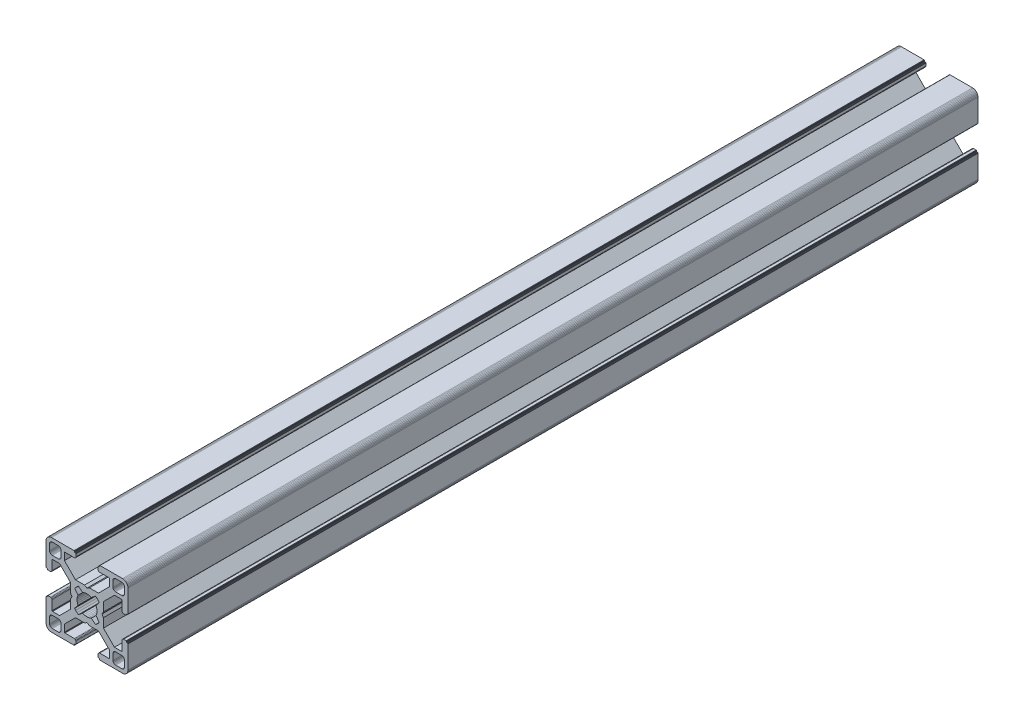
SolidWorks part; units mm, degrees
ref_plane "Front Plane" through (0, 0, 0) normal (0, 0, 1) x (1, 0, 0)
ref_plane "Top Plane" through (0, 0, 0) normal (0, 1, 0) x (1, 0, 0)
ref_plane "Right Plane" through (0, 0, 0) normal (1, 0, 0) x (0, 0, -1)
ref_plane "Plane1" through (0, 0, 0) normal (0, 0, 1) x (1, 0, 0)
sketch "Sketch1" plane through (0, 0, 0) normal (0, 0, 1) x (1, 0, 0)
  line L0 (28.3473, 29.9696) -> (28, 30)
  line L1 (28, 30) -> (19.75, 30)
  line L2 (19.75, 30) -> (19.7153, 29.997)
  line L3 (19.7153, 29.997) -> (19.6816, 29.9879)
  line L4 (19.6816, 29.9879) -> (19.65, 29.9732)
  line L5 (19.65, 29.9732) -> (19.6214, 29.9532)
  line L6 (19.6214, 29.9532) -> (19.5968, 29.9286)
  line L7 (19.5968, 29.9286) -> (19.5768, 29.9)
  line L8 (19.5768, 29.9) -> (19.5621, 29.8684)
  line L9 (19.5621, 29.8684) -> (19.553, 29.8347)
  line L10 (19.553, 29.8347) -> (19.55, 29.8)
  line L11 (19.55, 29.8) -> (19.55, 29.7)
  line L12 (19.55, 29.7) -> (19.547, 29.6653)
  line L13 (19.547, 29.6653) -> (19.5379, 29.6316)
  line L14 (19.5379, 29.6316) -> (19.5232, 29.6)
  line L15 (19.5232, 29.6) -> (19.5032, 29.5714)
  line L16 (19.5032, 29.5714) -> (19.4786, 29.5468)
  line L17 (19.4786, 29.5468) -> (19.45, 29.5268)
  line L18 (19.45, 29.5268) -> (19.4184, 29.5121)
  line L19 (19.4184, 29.5121) -> (19.3847, 29.503)
  line L20 (19.3847, 29.503) -> (19.35, 29.5)
  line L21 (19.35, 29.5) -> (19.25, 29.5)
  line L22 (19.25, 29.5) -> (19.2153, 29.497)
  line L23 (19.2153, 29.497) -> (19.1816, 29.4879)
  line L24 (19.1816, 29.4879) -> (19.15, 29.4732)
  line L25 (19.15, 29.4732) -> (19.1214, 29.4532)
  line L26 (19.1214, 29.4532) -> (19.0968, 29.4286)
  line L27 (19.0968, 29.4286) -> (19.0768, 29.4)
  line L28 (19.0768, 29.4) -> (19.0621, 29.3684)
  line L29 (19.0621, 29.3684) -> (19.053, 29.3347)
  line L30 (19.053, 29.3347) -> (19.05, 29.3)
  line L31 (19.05, 29.3) -> (19.05, 28.4)
  line L32 (19.05, 28.4) -> (19.0591, 28.2958)
  line L33 (19.0591, 28.2958) -> (19.0862, 28.1948)
  line L34 (19.0862, 28.1948) -> (19.1304, 28.1)
  line L35 (19.1304, 28.1) -> (19.1904, 28.0143)
  line L36 (19.1904, 28.0143) -> (19.2643, 27.9404)
  line L37 (19.2643, 27.9404) -> (19.35, 27.8804)
  line L38 (19.35, 27.8804) -> (19.4448, 27.8362)
  line L39 (19.4448, 27.8362) -> (19.5458, 27.8091)
  line L40 (19.5458, 27.8091) -> (19.65, 27.8)
  line L41 (19.65, 27.8) -> (23.05, 27.8)
  line L42 (23.05, 27.8) -> (23.0847, 27.7969)
  line L43 (23.0847, 27.7969) -> (23.1184, 27.7879)
  line L44 (23.1184, 27.7879) -> (23.15, 27.7732)
  line L45 (23.15, 27.7732) -> (23.1786, 27.7532)
  line L46 (23.1786, 27.7532) -> (23.2032, 27.7285)
  line L47 (23.2032, 27.7285) -> (23.2232, 27.7)
  line L48 (23.2232, 27.7) -> (23.2379, 27.6684)
  line L49 (23.2379, 27.6684) -> (23.247, 27.6347)
  line L50 (23.247, 27.6347) -> (23.25, 27.6)
  line L51 (23.25, 27.6) -> (23.25, 25.05)
  line L52 (23.25, 25.05) -> (19.2045, 21)
  line L53 (19.2045, 21) -> (15.9, 21)
  line L54 (15.9, 21) -> (15, 20.4848)
  line L55 (15, 20.4848) -> (14.1, 21)
  line L56 (14.1, 21) -> (10.7955, 21)
  line L57 (10.7955, 21) -> (7.9973, 23.8013)
  line L58 (7.9973, 23.8013) -> (6.75, 25.05)
  line L59 (6.75, 25.05) -> (6.75, 27.6)
  line L60 (6.75, 27.6) -> (6.753, 27.6347)
  line L61 (6.753, 27.6347) -> (6.7621, 27.6684)
  line L62 (6.7621, 27.6684) -> (6.7768, 27.7)
  line L63 (6.7768, 27.7) -> (6.7968, 27.7285)
  line L64 (6.7968, 27.7285) -> (6.8215, 27.7532)
  line L65 (6.8215, 27.7532) -> (6.85, 27.7732)
  line L66 (6.85, 27.7732) -> (6.8816, 27.7879)
  line L67 (6.8816, 27.7879) -> (6.9153, 27.7969)
  line L68 (6.9153, 27.7969) -> (6.95, 27.8)
  line L69 (6.95, 27.8) -> (10.35, 27.8)
  line L70 (10.35, 27.8) -> (10.4542, 27.8091)
  line L71 (10.4542, 27.8091) -> (10.5552, 27.8362)
  line L72 (10.5552, 27.8362) -> (10.65, 27.8804)
  line L73 (10.65, 27.8804) -> (10.7357, 27.9404)
  line L74 (10.7357, 27.9404) -> (10.8096, 28.0143)
  line L75 (10.8096, 28.0143) -> (10.8696, 28.1)
  line L76 (10.8696, 28.1) -> (10.9138, 28.1948)
  line L77 (10.9138, 28.1948) -> (10.9409, 28.2958)
  line L78 (10.9409, 28.2958) -> (10.95, 28.4)
  line L79 (10.95, 28.4) -> (10.95, 29.3)
  line L80 (10.95, 29.3) -> (10.947, 29.3347)
  line L81 (10.947, 29.3347) -> (10.938, 29.3684)
  line L82 (10.938, 29.3684) -> (10.9232, 29.4)
  line L83 (10.9232, 29.4) -> (10.9032, 29.4286)
  line L84 (10.9032, 29.4286) -> (10.8786, 29.4532)
  line L85 (10.8786, 29.4532) -> (10.85, 29.4732)
  line L86 (10.85, 29.4732) -> (10.8184, 29.4879)
  line L87 (10.8184, 29.4879) -> (10.7847, 29.497)
  line L88 (10.7847, 29.497) -> (10.75, 29.5)
  line L89 (10.75, 29.5) -> (10.65, 29.5)
  line L90 (10.65, 29.5) -> (10.6153, 29.503)
  line L91 (10.6153, 29.503) -> (10.5816, 29.5121)
  line L92 (10.5816, 29.5121) -> (10.55, 29.5268)
  line L93 (10.55, 29.5268) -> (10.5214, 29.5468)
  line L94 (10.5214, 29.5468) -> (10.4968, 29.5714)
  line L95 (10.4968, 29.5714) -> (10.4768, 29.6)
  line L96 (10.4768, 29.6) -> (10.4621, 29.6316)
  line L97 (10.4621, 29.6316) -> (10.453, 29.6653)
  line L98 (10.453, 29.6653) -> (10.45, 29.7)
  line L99 (10.45, 29.7) -> (10.45, 29.8)
  line L100 (10.45, 29.8) -> (10.447, 29.8347)
  line L101 (10.447, 29.8347) -> (10.4379, 29.8684)
  line L102 (10.4379, 29.8684) -> (10.4232, 29.9)
  line L103 (10.4232, 29.9) -> (10.4032, 29.9286)
  line L104 (10.4032, 29.9286) -> (10.3786, 29.9532)
  line L105 (10.3786, 29.9532) -> (10.35, 29.9732)
  line L106 (10.35, 29.9732) -> (10.3184, 29.9879)
  line L107 (10.3184, 29.9879) -> (10.2847, 29.997)
  line L108 (10.2847, 29.997) -> (10.25, 30)
  line L109 (10.25, 30) -> (2, 30)
  line L110 (2, 30) -> (1.6527, 29.9696)
  line L111 (1.6527, 29.9696) -> (1.316, 29.8794)
  line L112 (1.316, 29.8794) -> (1, 29.7321)
  line L113 (1, 29.7321) -> (0.7144, 29.5321)
  line L114 (0.7144, 29.5321) -> (0.4679, 29.2856)
  line L115 (0.4679, 29.2856) -> (0.2679, 29)
  line L116 (0.2679, 29) -> (0.1206, 28.684)
  line L117 (0.1206, 28.684) -> (0.0304, 28.3473)
  line L118 (0.0304, 28.3473) -> (0, 28)
  line L119 (0, 28) -> (0, 19.75)
  line L120 (0, 19.75) -> (0.003, 19.7153)
  line L121 (0.003, 19.7153) -> (0.0121, 19.6816)
  line L122 (0.0121, 19.6816) -> (0.0268, 19.65)
  line L123 (0.0268, 19.65) -> (0.0468, 19.6214)
  line L124 (0.0468, 19.6214) -> (0.0714, 19.5968)
  line L125 (0.0714, 19.5968) -> (0.1, 19.5768)
  line L126 (0.1, 19.5768) -> (0.1316, 19.5621)
  line L127 (0.1316, 19.5621) -> (0.1653, 19.553)
  line L128 (0.1653, 19.553) -> (0.2, 19.55)
  line L129 (0.2, 19.55) -> (0.3, 19.55)
  line L130 (0.3, 19.55) -> (0.3347, 19.547)
  line L131 (0.3347, 19.547) -> (0.3684, 19.5379)
  line L132 (0.3684, 19.5379) -> (0.4, 19.5232)
  line L133 (0.4, 19.5232) -> (0.4286, 19.5032)
  line L134 (0.4286, 19.5032) -> (0.4532, 19.4786)
  line L135 (0.4532, 19.4786) -> (0.4732, 19.45)
  line L136 (0.4732, 19.45) -> (0.4879, 19.4184)
  line L137 (0.4879, 19.4184) -> (0.497, 19.3847)
  line L138 (0.497, 19.3847) -> (0.5, 19.35)
  line L139 (0.5, 19.35) -> (0.5, 19.25)
  line L140 (0.5, 19.25) -> (0.503, 19.2153)
  line L141 (0.503, 19.2153) -> (0.5121, 19.1816)
  line L142 (0.5121, 19.1816) -> (0.5268, 19.15)
  line L143 (0.5268, 19.15) -> (0.5468, 19.1214)
  line L144 (0.5468, 19.1214) -> (0.5714, 19.0968)
  line L145 (0.5714, 19.0968) -> (0.6, 19.0768)
  line L146 (0.6, 19.0768) -> (0.6316, 19.0621)
  line L147 (0.6316, 19.0621) -> (0.6653, 19.053)
  line L148 (0.6653, 19.053) -> (0.7, 19.05)
  line L149 (0.7, 19.05) -> (1.6, 19.05)
  line L150 (1.6, 19.05) -> (1.7042, 19.0591)
  line L151 (1.7042, 19.0591) -> (1.8052, 19.0862)
  line L152 (1.8052, 19.0862) -> (1.9, 19.1304)
  line L153 (1.9, 19.1304) -> (1.9857, 19.1904)
  line L154 (1.9857, 19.1904) -> (2.0596, 19.2643)
  line L155 (2.0596, 19.2643) -> (2.1196, 19.35)
  line L156 (2.1196, 19.35) -> (2.1638, 19.4448)
  line L157 (2.1638, 19.4448) -> (2.1909, 19.5458)
  line L158 (2.1909, 19.5458) -> (2.2, 19.65)
  line L159 (2.2, 19.65) -> (2.2, 23.05)
  line L160 (2.2, 23.05) -> (2.203, 23.0847)
  line L161 (2.203, 23.0847) -> (2.2121, 23.1184)
  line L162 (2.2121, 23.1184) -> (2.2268, 23.15)
  line L163 (2.2268, 23.15) -> (2.2468, 23.1786)
  line L164 (2.2468, 23.1786) -> (2.2714, 23.2032)
  line L165 (2.2714, 23.2032) -> (2.3, 23.2232)
  line L166 (2.3, 23.2232) -> (2.3316, 23.2379)
  line L167 (2.3316, 23.2379) -> (2.3653, 23.247)
  line L168 (2.3653, 23.247) -> (2.4, 23.25)
  line L169 (2.4, 23.25) -> (4.95, 23.25)
  line L170 (4.95, 23.25) -> (7.9973, 20.2027)
  line L171 (7.9973, 20.2027) -> (8.9955, 19.2045)
  line L172 (8.9955, 19.2045) -> (8.9955, 15.9)
  line L173 (8.9955, 15.9) -> (9.5151, 15)
  line L174 (9.5151, 15) -> (8.9955, 14.1)
  line L175 (8.9955, 14.1) -> (8.9955, 10.7955)
  line L176 (8.9955, 10.7955) -> (4.95, 6.75)
  line L177 (4.95, 6.75) -> (2.4, 6.75)
  line L178 (2.4, 6.75) -> (2.3653, 6.753)
  line L179 (2.3653, 6.753) -> (2.3316, 6.7621)
  line L180 (2.3316, 6.7621) -> (2.3, 6.7768)
  line L181 (2.3, 6.7768) -> (2.2714, 6.7968)
  line L182 (2.2714, 6.7968) -> (2.2468, 6.8214)
  line L183 (2.2468, 6.8214) -> (2.2268, 6.85)
  line L184 (2.2268, 6.85) -> (2.2121, 6.8816)
  line L185 (2.2121, 6.8816) -> (2.203, 6.9153)
  line L186 (2.203, 6.9153) -> (2.2, 6.95)
  line L187 (2.2, 6.95) -> (2.2, 10.35)
  line L188 (2.2, 10.35) -> (2.1909, 10.4542)
  line L189 (2.1909, 10.4542) -> (2.1638, 10.5552)
  line L190 (2.1638, 10.5552) -> (2.1196, 10.65)
  line L191 (2.1196, 10.65) -> (2.0596, 10.7357)
  line L192 (2.0596, 10.7357) -> (1.9857, 10.8096)
  line L193 (1.9857, 10.8096) -> (1.9, 10.8696)
  line L194 (1.9, 10.8696) -> (1.8052, 10.9138)
  line L195 (1.8052, 10.9138) -> (1.7042, 10.9409)
  line L196 (1.7042, 10.9409) -> (1.6, 10.95)
  line L197 (1.6, 10.95) -> (0.7, 10.95)
  line L198 (0.7, 10.95) -> (0.6653, 10.9469)
  line L199 (0.6653, 10.9469) -> (0.6316, 10.9379)
  line L200 (0.6316, 10.9379) -> (0.6, 10.9232)
  line L201 (0.6, 10.9232) -> (0.5715, 10.9032)
  line L202 (0.5715, 10.9032) -> (0.5468, 10.8785)
  line L203 (0.5468, 10.8785) -> (0.5268, 10.85)
  line L204 (0.5268, 10.85) -> (0.5121, 10.8184)
  line L205 (0.5121, 10.8184) -> (0.503, 10.7847)
  line L206 (0.503, 10.7847) -> (0.5, 10.75)
  line L207 (0.5, 10.75) -> (0.5, 10.65)
  line L208 (0.5, 10.65) -> (0.497, 10.6153)
  line L209 (0.497, 10.6153) -> (0.4879, 10.5816)
  line L210 (0.4879, 10.5816) -> (0.4732, 10.55)
  line L211 (0.4732, 10.55) -> (0.4532, 10.5214)
  line L212 (0.4532, 10.5214) -> (0.4286, 10.4968)
  line L213 (0.4286, 10.4968) -> (0.4, 10.4768)
  line L214 (0.4, 10.4768) -> (0.3684, 10.4621)
  line L215 (0.3684, 10.4621) -> (0.3347, 10.453)
  line L216 (0.3347, 10.453) -> (0.3, 10.45)
  line L217 (0.3, 10.45) -> (0.2, 10.45)
  line L218 (0.2, 10.45) -> (0.1653, 10.447)
  line L219 (0.1653, 10.447) -> (0.1316, 10.4379)
  line L220 (0.1316, 10.4379) -> (0.1, 10.4232)
  line L221 (0.1, 10.4232) -> (0.0714, 10.4032)
  line L222 (0.0714, 10.4032) -> (0.0468, 10.3786)
  line L223 (0.0468, 10.3786) -> (0.0268, 10.35)
  line L224 (0.0268, 10.35) -> (0.0121, 10.3184)
  line L225 (0.0121, 10.3184) -> (0.003, 10.2847)
  line L226 (0.003, 10.2847) -> (0, 10.25)
  line L227 (0, 10.25) -> (0, 2)
  line L228 (0, 2) -> (0.0304, 1.6527)
  line L229 (0.0304, 1.6527) -> (0.1206, 1.316)
  line L230 (0.1206, 1.316) -> (0.2679, 1)
  line L231 (0.2679, 1) -> (0.4679, 0.7144)
  line L232 (0.4679, 0.7144) -> (0.7144, 0.4679)
  line L233 (0.7144, 0.4679) -> (1, 0.2679)
  line L234 (1, 0.2679) -> (1.316, 0.1206)
  line L235 (1.316, 0.1206) -> (1.6527, 0.0304)
  line L236 (1.6527, 0.0304) -> (2, 0)
  line L237 (2, 0) -> (10.25, 0)
  line L238 (10.25, 0) -> (10.2847, 0.003)
  line L239 (10.2847, 0.003) -> (10.3184, 0.0121)
  line L240 (10.3184, 0.0121) -> (10.35, 0.0268)
  line L241 (10.35, 0.0268) -> (10.3786, 0.0468)
  line L242 (10.3786, 0.0468) -> (10.4032, 0.0714)
  line L243 (10.4032, 0.0714) -> (10.4232, 0.1)
  line L244 (10.4232, 0.1) -> (10.4379, 0.1316)
  line L245 (10.4379, 0.1316) -> (10.447, 0.1653)
  line L246 (10.447, 0.1653) -> (10.45, 0.2)
  line L247 (10.45, 0.2) -> (10.45, 0.3)
  line L248 (10.45, 0.3) -> (10.453, 0.3347)
  line L249 (10.453, 0.3347) -> (10.4621, 0.3684)
  line L250 (10.4621, 0.3684) -> (10.4768, 0.4)
  line L251 (10.4768, 0.4) -> (10.4968, 0.4286)
  line L252 (10.4968, 0.4286) -> (10.5214, 0.4532)
  line L253 (10.5214, 0.4532) -> (10.55, 0.4732)
  line L254 (10.55, 0.4732) -> (10.5816, 0.4879)
  line L255 (10.5816, 0.4879) -> (10.6153, 0.497)
  line L256 (10.6153, 0.497) -> (10.65, 0.5)
  line L257 (10.65, 0.5) -> (10.75, 0.5)
  line L258 (10.75, 0.5) -> (10.7847, 0.503)
  line L259 (10.7847, 0.503) -> (10.8184, 0.5121)
  line L260 (10.8184, 0.5121) -> (10.85, 0.5268)
  line L261 (10.85, 0.5268) -> (10.8785, 0.5468)
  line L262 (10.8785, 0.5468) -> (10.9032, 0.5715)
  line L263 (10.9032, 0.5715) -> (10.9232, 0.6)
  line L264 (10.9232, 0.6) -> (10.9379, 0.6316)
  line L265 (10.9379, 0.6316) -> (10.9469, 0.6653)
  line L266 (10.9469, 0.6653) -> (10.95, 0.7)
  line L267 (10.95, 0.7) -> (10.95, 1.6)
  line L268 (10.95, 1.6) -> (10.9409, 1.7042)
  line L269 (10.9409, 1.7042) -> (10.9138, 1.8052)
  line L270 (10.9138, 1.8052) -> (10.8696, 1.9)
  line L271 (10.8696, 1.9) -> (10.8096, 1.9857)
  line L272 (10.8096, 1.9857) -> (10.7357, 2.0596)
  line L273 (10.7357, 2.0596) -> (10.65, 2.1196)
  line L274 (10.65, 2.1196) -> (10.5552, 2.1638)
  line L275 (10.5552, 2.1638) -> (10.4542, 2.1909)
  line L276 (10.4542, 2.1909) -> (10.35, 2.2)
  line L277 (10.35, 2.2) -> (6.95, 2.2)
  line L278 (6.95, 2.2) -> (6.9153, 2.203)
  line L279 (6.9153, 2.203) -> (6.8816, 2.212)
  line L280 (6.8816, 2.212) -> (6.85, 2.2268)
  line L281 (6.85, 2.2268) -> (6.8215, 2.2468)
  line L282 (6.8215, 2.2468) -> (6.7968, 2.2714)
  line L283 (6.7968, 2.2714) -> (6.7768, 2.3)
  line L284 (6.7768, 2.3) -> (6.7621, 2.3316)
  line L285 (6.7621, 2.3316) -> (6.753, 2.3653)
  line L286 (6.753, 2.3653) -> (6.75, 2.4)
  line L287 (6.75, 2.4) -> (6.75, 4.95)
  line L288 (6.75, 4.95) -> (9.7875, 7.9908)
  line L289 (9.7875, 7.9908) -> (10.7955, 9)
  line L290 (10.7955, 9) -> (14.1, 9)
  line L291 (14.1, 9) -> (15, 9.5151)
  line L292 (15, 9.5151) -> (15.9, 9)
  line L293 (15.9, 9) -> (19.2045, 9)
  line L294 (19.2045, 9) -> (20.2126, 7.9908)
  line L295 (20.2126, 7.9908) -> (23.25, 4.95)
  line L296 (23.25, 4.95) -> (23.25, 2.4)
  line L297 (23.25, 2.4) -> (23.247, 2.3653)
  line L298 (23.247, 2.3653) -> (23.2379, 2.3316)
  line L299 (23.2379, 2.3316) -> (23.2232, 2.3)
  line L300 (23.2232, 2.3) -> (23.2032, 2.2714)
  line L301 (23.2032, 2.2714) -> (23.1786, 2.2468)
  line L302 (23.1786, 2.2468) -> (23.15, 2.2268)
  line L303 (23.15, 2.2268) -> (23.1184, 2.212)
  line L304 (23.1184, 2.212) -> (23.0847, 2.203)
  line L305 (23.0847, 2.203) -> (23.05, 2.2)
  line L306 (23.05, 2.2) -> (19.65, 2.2)
  line L307 (19.65, 2.2) -> (19.5458, 2.1909)
  line L308 (19.5458, 2.1909) -> (19.4448, 2.1638)
  line L309 (19.4448, 2.1638) -> (19.35, 2.1196)
  line L310 (19.35, 2.1196) -> (19.2643, 2.0596)
  line L311 (19.2643, 2.0596) -> (19.1904, 1.9857)
  line L312 (19.1904, 1.9857) -> (19.1304, 1.9)
  line L313 (19.1304, 1.9) -> (19.0862, 1.8052)
  line L314 (19.0862, 1.8052) -> (19.0591, 1.7042)
  line L315 (19.0591, 1.7042) -> (19.05, 1.6)
  line L316 (19.05, 1.6) -> (19.05, 0.7)
  line L317 (19.05, 0.7) -> (19.053, 0.6653)
  line L318 (19.053, 0.6653) -> (19.0621, 0.6316)
  line L319 (19.0621, 0.6316) -> (19.0768, 0.6)
  line L320 (19.0768, 0.6) -> (19.0968, 0.5714)
  line L321 (19.0968, 0.5714) -> (19.1214, 0.5468)
  line L322 (19.1214, 0.5468) -> (19.15, 0.5268)
  line L323 (19.15, 0.5268) -> (19.1816, 0.5121)
  line L324 (19.1816, 0.5121) -> (19.2153, 0.503)
  line L325 (19.2153, 0.503) -> (19.25, 0.5)
  line L326 (19.25, 0.5) -> (19.35, 0.5)
  line L327 (19.35, 0.5) -> (19.3847, 0.497)
  line L328 (19.3847, 0.497) -> (19.4184, 0.4879)
  line L329 (19.4184, 0.4879) -> (19.45, 0.4732)
  line L330 (19.45, 0.4732) -> (19.4786, 0.4532)
  line L331 (19.4786, 0.4532) -> (19.5032, 0.4286)
  line L332 (19.5032, 0.4286) -> (19.5232, 0.4)
  line L333 (19.5232, 0.4) -> (19.5379, 0.3684)
  line L334 (19.5379, 0.3684) -> (19.547, 0.3347)
  line L335 (19.547, 0.3347) -> (19.55, 0.3)
  line L336 (19.55, 0.3) -> (19.55, 0.2)
  line L337 (19.55, 0.2) -> (19.553, 0.1653)
  line L338 (19.553, 0.1653) -> (19.5621, 0.1316)
  line L339 (19.5621, 0.1316) -> (19.5768, 0.1)
  line L340 (19.5768, 0.1) -> (19.5968, 0.0714)
  line L341 (19.5968, 0.0714) -> (19.6214, 0.0468)
  line L342 (19.6214, 0.0468) -> (19.65, 0.0268)
  line L343 (19.65, 0.0268) -> (19.6816, 0.0121)
  line L344 (19.6816, 0.0121) -> (19.7153, 0.003)
  line L345 (19.7153, 0.003) -> (19.75, 0)
  line L346 (19.75, 0) -> (28, 0)
  line L347 (28, 0) -> (28.3473, 0.0304)
  line L348 (28.3473, 0.0304) -> (28.684, 0.1206)
  line L349 (28.684, 0.1206) -> (29, 0.2679)
  line L350 (29, 0.2679) -> (29.2856, 0.4679)
  line L351 (29.2856, 0.4679) -> (29.5321, 0.7144)
  line L352 (29.5321, 0.7144) -> (29.7321, 1)
  line L353 (29.7321, 1) -> (29.8794, 1.316)
  line L354 (29.8794, 1.316) -> (29.9696, 1.6527)
  line L355 (29.9696, 1.6527) -> (30, 2)
  line L356 (30, 2) -> (30, 10.25)
  line L357 (30, 10.25) -> (29.997, 10.2847)
  line L358 (29.997, 10.2847) -> (29.988, 10.3184)
  line L359 (29.988, 10.3184) -> (29.9732, 10.35)
  line L360 (29.9732, 10.35) -> (29.9532, 10.3785)
  line L361 (29.9532, 10.3785) -> (29.9286, 10.4032)
  line L362 (29.9286, 10.4032) -> (29.9, 10.4232)
  line L363 (29.9, 10.4232) -> (29.8684, 10.4379)
  line L364 (29.8684, 10.4379) -> (29.8347, 10.447)
  line L365 (29.8347, 10.447) -> (29.8, 10.45)
  line L366 (29.8, 10.45) -> (29.7, 10.45)
  line L367 (29.7, 10.45) -> (29.6649, 10.4534)
  line L368 (29.6649, 10.4534) -> (29.6312, 10.4624)
  line L369 (29.6312, 10.4624) -> (29.5996, 10.4772)
  line L370 (29.5996, 10.4772) -> (29.5711, 10.4972)
  line L371 (29.5711, 10.4972) -> (29.5464, 10.5218)
  line L372 (29.5464, 10.5218) -> (29.5264, 10.5504)
  line L373 (29.5264, 10.5504) -> (29.5117, 10.582)
  line L374 (29.5117, 10.582) -> (29.5027, 10.6156)
  line L375 (29.5027, 10.6156) -> (29.4996, 10.6504)
  line L376 (29.4996, 10.6504) -> (29.4996, 10.7504)
  line L377 (29.4996, 10.7504) -> (29.497, 10.7847)
  line L378 (29.497, 10.7847) -> (29.4879, 10.8184)
  line L379 (29.4879, 10.8184) -> (29.4732, 10.85)
  line L380 (29.4732, 10.85) -> (29.4532, 10.8785)
  line L381 (29.4532, 10.8785) -> (29.4286, 10.9032)
  line L382 (29.4286, 10.9032) -> (29.4, 10.9232)
  line L383 (29.4, 10.9232) -> (29.3684, 10.9379)
  line L384 (29.3684, 10.9379) -> (29.3347, 10.9469)
  line L385 (29.3347, 10.9469) -> (29.3, 10.95)
  line L386 (29.3, 10.95) -> (28.4, 10.95)
  line L387 (28.4, 10.95) -> (28.2958, 10.9409)
  line L388 (28.2958, 10.9409) -> (28.1948, 10.9138)
  line L389 (28.1948, 10.9138) -> (28.1, 10.8696)
  line L390 (28.1, 10.8696) -> (28.0143, 10.8096)
  line L391 (28.0143, 10.8096) -> (27.9404, 10.7357)
  line L392 (27.9404, 10.7357) -> (27.8804, 10.65)
  line L393 (27.8804, 10.65) -> (27.8362, 10.5552)
  line L394 (27.8362, 10.5552) -> (27.8091, 10.4542)
  line L395 (27.8091, 10.4542) -> (27.8, 10.35)
  line L396 (27.8, 10.35) -> (27.8, 6.95)
  line L397 (27.8, 6.95) -> (27.797, 6.9153)
  line L398 (27.797, 6.9153) -> (27.7879, 6.8816)
  line L399 (27.7879, 6.8816) -> (27.7732, 6.85)
  line L400 (27.7732, 6.85) -> (27.7532, 6.8214)
  line L401 (27.7532, 6.8214) -> (27.7286, 6.7968)
  line L402 (27.7286, 6.7968) -> (27.7, 6.7768)
  line L403 (27.7, 6.7768) -> (27.6684, 6.7621)
  line L404 (27.6684, 6.7621) -> (27.6347, 6.753)
  line L405 (27.6347, 6.753) -> (27.6, 6.75)
  line L406 (27.6, 6.75) -> (25.05, 6.75)
  line L407 (25.05, 6.75) -> (23.8092, 7.9908)
  line L408 (23.8092, 7.9908) -> (21.0045, 10.7955)
  line L409 (21.0045, 10.7955) -> (21.0045, 14.1)
  line L410 (21.0045, 14.1) -> (20.4849, 15)
  line L411 (20.4849, 15) -> (21.0045, 15.9)
  line L412 (21.0045, 15.9) -> (21.0045, 19.2045)
  line L413 (21.0045, 19.2045) -> (25.05, 23.25)
  line L414 (25.05, 23.25) -> (27.6, 23.25)
  line L415 (27.6, 23.25) -> (27.6347, 23.247)
  line L416 (27.6347, 23.247) -> (27.6684, 23.2379)
  line L417 (27.6684, 23.2379) -> (27.7, 23.2232)
  line L418 (27.7, 23.2232) -> (27.7286, 23.2032)
  line L419 (27.7286, 23.2032) -> (27.7532, 23.1786)
  line L420 (27.7532, 23.1786) -> (27.7732, 23.15)
  line L421 (27.7732, 23.15) -> (27.7879, 23.1184)
  line L422 (27.7879, 23.1184) -> (27.797, 23.0847)
  line L423 (27.797, 23.0847) -> (27.8, 23.05)
  line L424 (27.8, 23.05) -> (27.8, 19.65)
  line L425 (27.8, 19.65) -> (27.8091, 19.5458)
  line L426 (27.8091, 19.5458) -> (27.8362, 19.4448)
  line L427 (27.8362, 19.4448) -> (27.8804, 19.35)
  line L428 (27.8804, 19.35) -> (27.9404, 19.2643)
  line L429 (27.9404, 19.2643) -> (28.0143, 19.1904)
  line L430 (28.0143, 19.1904) -> (28.1, 19.1304)
  line L431 (28.1, 19.1304) -> (28.1948, 19.0862)
  line L432 (28.1948, 19.0862) -> (28.2958, 19.0591)
  line L433 (28.2958, 19.0591) -> (28.4, 19.05)
  line L434 (28.4, 19.05) -> (29.3, 19.05)
  line L435 (29.3, 19.05) -> (29.3347, 19.053)
  line L436 (29.3347, 19.053) -> (29.3684, 19.0621)
  line L437 (29.3684, 19.0621) -> (29.4, 19.0768)
  line L438 (29.4, 19.0768) -> (29.4282, 19.0971)
  line L439 (29.4282, 19.0971) -> (29.4528, 19.1218)
  line L440 (29.4528, 19.1218) -> (29.4728, 19.1504)
  line L441 (29.4728, 19.1504) -> (29.4876, 19.182)
  line L442 (29.4876, 19.182) -> (29.4966, 19.2156)
  line L443 (29.4966, 19.2156) -> (29.4996, 19.2504)
  line L444 (29.4996, 19.2504) -> (29.4996, 19.3504)
  line L445 (29.4996, 19.3504) -> (29.5027, 19.3851)
  line L446 (29.5027, 19.3851) -> (29.5117, 19.4188)
  line L447 (29.5117, 19.4188) -> (29.5264, 19.4504)
  line L448 (29.5264, 19.4504) -> (29.5464, 19.4789)
  line L449 (29.5464, 19.4789) -> (29.5711, 19.5036)
  line L450 (29.5711, 19.5036) -> (29.5996, 19.5236)
  line L451 (29.5996, 19.5236) -> (29.6312, 19.5383)
  line L452 (29.6312, 19.5383) -> (29.6649, 19.5473)
  line L453 (29.6649, 19.5473) -> (29.7, 19.55)
  line L454 (29.7, 19.55) -> (29.8, 19.55)
  line L455 (29.8, 19.55) -> (29.8347, 19.553)
  line L456 (29.8347, 19.553) -> (29.8684, 19.5621)
  line L457 (29.8684, 19.5621) -> (29.9, 19.5768)
  line L458 (29.9, 19.5768) -> (29.9286, 19.5968)
  line L459 (29.9286, 19.5968) -> (29.9532, 19.6214)
  line L460 (29.9532, 19.6214) -> (29.9732, 19.65)
  line L461 (29.9732, 19.65) -> (29.9879, 19.6816)
  line L462 (29.9879, 19.6816) -> (29.997, 19.7153)
  line L463 (29.997, 19.7153) -> (30, 19.75)
  line L464 (30, 19.75) -> (30, 28)
  line L465 (30, 28) -> (29.9696, 28.3473)
  line L466 (29.9696, 28.3473) -> (29.8794, 28.684)
  line L467 (29.8794, 28.684) -> (29.7321, 29)
  line L468 (29.7321, 29) -> (29.5321, 29.2856)
  line L469 (29.5321, 29.2856) -> (29.2856, 29.5321)
  line L470 (29.2856, 29.5321) -> (29, 29.7321)
  line L471 (29, 29.7321) -> (28.684, 29.8794)
  line L472 (28.684, 29.8794) -> (28.3473, 29.9696)
  line L473 (1.3, 25.5) -> (1.3, 27.7)
  line L474 (1.3, 27.7) -> (1.3123, 27.8564)
  line L475 (1.3123, 27.8564) -> (1.3489, 28.009)
  line L476 (1.3489, 28.009) -> (1.409, 28.154)
  line L477 (1.409, 28.154) -> (1.491, 28.2878)
  line L478 (1.491, 28.2878) -> (1.5929, 28.4071)
  line L479 (1.5929, 28.4071) -> (1.7122, 28.509)
  line L480 (1.7122, 28.509) -> (1.846, 28.591)
  line L481 (1.846, 28.591) -> (1.991, 28.6511)
  line L482 (1.991, 28.6511) -> (2.1436, 28.6877)
  line L483 (2.1436, 28.6877) -> (2.3, 28.7)
  line L484 (2.3, 28.7) -> (4.5, 28.7)
  line L485 (4.5, 28.7) -> (4.6564, 28.6877)
  line L486 (4.6564, 28.6877) -> (4.809, 28.6511)
  line L487 (4.809, 28.6511) -> (4.954, 28.591)
  line L488 (4.954, 28.591) -> (5.0878, 28.509)
  line L489 (5.0878, 28.509) -> (5.2071, 28.4071)
  line L490 (5.2071, 28.4071) -> (5.309, 28.2878)
  line L491 (5.309, 28.2878) -> (5.391, 28.154)
  line L492 (5.391, 28.154) -> (5.4511, 28.009)
  line L493 (5.4511, 28.009) -> (5.4877, 27.8564)
  line L494 (5.4877, 27.8564) -> (5.5, 27.7)
  line L495 (5.5, 27.7) -> (5.5, 25.5)
  line L496 (5.5, 25.5) -> (5.4877, 25.3436)
  line L497 (5.4877, 25.3436) -> (5.4511, 25.191)
  line L498 (5.4511, 25.191) -> (5.391, 25.046)
  line L499 (5.391, 25.046) -> (5.309, 24.9122)
  line L500 (5.309, 24.9122) -> (5.2071, 24.7929)
  line L501 (5.2071, 24.7929) -> (5.0878, 24.691)
  line L502 (5.0878, 24.691) -> (4.954, 24.609)
  line L503 (4.954, 24.609) -> (4.809, 24.5489)
  line L504 (4.809, 24.5489) -> (4.6564, 24.5123)
  line L505 (4.6564, 24.5123) -> (4.5, 24.5)
  line L506 (4.5, 24.5) -> (2.3, 24.5)
  line L507 (2.3, 24.5) -> (2.1436, 24.5123)
  line L508 (2.1436, 24.5123) -> (1.991, 24.5489)
  line L509 (1.991, 24.5489) -> (1.846, 24.609)
  line L510 (1.846, 24.609) -> (1.7122, 24.691)
  line L511 (1.7122, 24.691) -> (1.5929, 24.7929)
  line L512 (1.5929, 24.7929) -> (1.491, 24.9122)
  line L513 (1.491, 24.9122) -> (1.409, 25.046)
  line L514 (1.409, 25.046) -> (1.3489, 25.191)
  line L515 (1.3489, 25.191) -> (1.3123, 25.3436)
  line L516 (1.3123, 25.3436) -> (1.3, 25.5)
  line L517 (25.3436, 28.6877) -> (25.5, 28.7)
  line L518 (25.5, 28.7) -> (27.7, 28.7)
  line L519 (27.7, 28.7) -> (27.8564, 28.6877)
  line L520 (27.8564, 28.6877) -> (28.009, 28.6511)
  line L521 (28.009, 28.6511) -> (28.154, 28.591)
  line L522 (28.154, 28.591) -> (28.2878, 28.509)
  line L523 (28.2878, 28.509) -> (28.4071, 28.4071)
  line L524 (28.4071, 28.4071) -> (28.509, 28.2878)
  line L525 (28.509, 28.2878) -> (28.591, 28.154)
  line L526 (28.591, 28.154) -> (28.6511, 28.009)
  line L527 (28.6511, 28.009) -> (28.6877, 27.8564)
  line L528 (28.6877, 27.8564) -> (28.7, 27.7)
  line L529 (28.7, 27.7) -> (28.7, 25.5)
  line L530 (28.7, 25.5) -> (28.6877, 25.3436)
  line L531 (28.6877, 25.3436) -> (28.6511, 25.191)
  line L532 (28.6511, 25.191) -> (28.591, 25.046)
  line L533 (28.591, 25.046) -> (28.509, 24.9122)
  line L534 (28.509, 24.9122) -> (28.4071, 24.7929)
  line L535 (28.4071, 24.7929) -> (28.2878, 24.691)
  line L536 (28.2878, 24.691) -> (28.154, 24.609)
  line L537 (28.154, 24.609) -> (28.009, 24.5489)
  line L538 (28.009, 24.5489) -> (27.8564, 24.5123)
  line L539 (27.8564, 24.5123) -> (27.7, 24.5)
  line L540 (27.7, 24.5) -> (25.5, 24.5)
  line L541 (25.5, 24.5) -> (25.3436, 24.5123)
  line L542 (25.3436, 24.5123) -> (25.191, 24.5489)
  line L543 (25.191, 24.5489) -> (25.046, 24.609)
  line L544 (25.046, 24.609) -> (24.9122, 24.691)
  line L545 (24.9122, 24.691) -> (24.7929, 24.7929)
  line L546 (24.7929, 24.7929) -> (24.691, 24.9122)
  line L547 (24.691, 24.9122) -> (24.609, 25.046)
  line L548 (24.609, 25.046) -> (24.5489, 25.191)
  line L549 (24.5489, 25.191) -> (24.5123, 25.3436)
  line L550 (24.5123, 25.3436) -> (24.5, 25.5)
  line L551 (24.5, 25.5) -> (24.5, 27.7)
  line L552 (24.5, 27.7) -> (24.5123, 27.8564)
  line L553 (24.5123, 27.8564) -> (24.5489, 28.009)
  line L554 (24.5489, 28.009) -> (24.609, 28.154)
  line L555 (24.609, 28.154) -> (24.691, 28.2878)
  line L556 (24.691, 28.2878) -> (24.7929, 28.4071)
  line L557 (24.7929, 28.4071) -> (24.9122, 28.509)
  line L558 (24.9122, 28.509) -> (25.046, 28.591)
  line L559 (25.046, 28.591) -> (25.191, 28.6511)
  line L560 (25.191, 28.6511) -> (25.3436, 28.6877)
  line L561 (15, 18.65) -> (15.55, 18.6083)
  line L562 (15.55, 18.6083) -> (16.0875, 18.4842)
  line L563 (16.0875, 18.4842) -> (16.6001, 18.2806)
  line L564 (16.6001, 18.2806) -> (18.1359, 19.5184)
  line L565 (18.1359, 19.5184) -> (18.645, 19.1187)
  line L566 (18.645, 19.1187) -> (19.1036, 18.6621)
  line L567 (19.1036, 18.6621) -> (19.5053, 18.1547)
  line L568 (19.5053, 18.1547) -> (18.2806, 16.6001)
  line L569 (18.2806, 16.6001) -> (18.4842, 16.0875)
  line L570 (18.4842, 16.0875) -> (18.6083, 15.55)
  line L571 (18.6083, 15.55) -> (18.65, 15)
  line L572 (18.65, 15) -> (18.6083, 14.45)
  line L573 (18.6083, 14.45) -> (18.4842, 13.9125)
  line L574 (18.4842, 13.9125) -> (18.2806, 13.3999)
  line L575 (18.2806, 13.3999) -> (19.5053, 11.8453)
  line L576 (19.5053, 11.8453) -> (19.1036, 11.3379)
  line L577 (19.1036, 11.3379) -> (18.645, 10.8813)
  line L578 (18.645, 10.8813) -> (18.1359, 10.4816)
  line L579 (18.1359, 10.4816) -> (16.6001, 11.7194)
  line L580 (16.6001, 11.7194) -> (16.0875, 11.5158)
  line L581 (16.0875, 11.5158) -> (15.55, 11.3917)
  line L582 (15.55, 11.3917) -> (15, 11.35)
  line L583 (15, 11.35) -> (14.45, 11.3917)
  line L584 (14.45, 11.3917) -> (13.9125, 11.5158)
  line L585 (13.9125, 11.5158) -> (13.3999, 11.7194)
  line L586 (13.3999, 11.7194) -> (11.8641, 10.4816)
  line L587 (11.8641, 10.4816) -> (11.355, 10.8813)
  line L588 (11.355, 10.8813) -> (10.8964, 11.3379)
  line L589 (10.8964, 11.3379) -> (10.4947, 11.8453)
  line L590 (10.4947, 11.8453) -> (11.7194, 13.3999)
  line L591 (11.7194, 13.3999) -> (11.5158, 13.9125)
  line L592 (11.5158, 13.9125) -> (11.3917, 14.45)
  line L593 (11.3917, 14.45) -> (11.35, 15)
  line L594 (11.35, 15) -> (11.3917, 15.55)
  line L595 (11.3917, 15.55) -> (11.5158, 16.0875)
  line L596 (11.5158, 16.0875) -> (11.7194, 16.6001)
  line L597 (11.7194, 16.6001) -> (10.4947, 18.1547)
  line L598 (10.4947, 18.1547) -> (10.8964, 18.6621)
  line L599 (10.8964, 18.6621) -> (11.355, 19.1187)
  line L600 (11.355, 19.1187) -> (11.8641, 19.5184)
  line L601 (11.8641, 19.5184) -> (13.3999, 18.2806)
  line L602 (13.3999, 18.2806) -> (13.9125, 18.4842)
  line L603 (13.9125, 18.4842) -> (14.45, 18.6083)
  line L604 (14.45, 18.6083) -> (15, 18.65)
  line L605 (4.5, 1.3) -> (2.3, 1.3)
  line L606 (2.3, 1.3) -> (2.1436, 1.3123)
  line L607 (2.1436, 1.3123) -> (1.991, 1.3489)
  line L608 (1.991, 1.3489) -> (1.846, 1.409)
  line L609 (1.846, 1.409) -> (1.7122, 1.491)
  line L610 (1.7122, 1.491) -> (1.5929, 1.5929)
  line L611 (1.5929, 1.5929) -> (1.491, 1.7122)
  line L612 (1.491, 1.7122) -> (1.409, 1.846)
  line L613 (1.409, 1.846) -> (1.3489, 1.991)
  line L614 (1.3489, 1.991) -> (1.3123, 2.1436)
  line L615 (1.3123, 2.1436) -> (1.3, 2.3)
  line L616 (1.3, 2.3) -> (1.3, 4.5)
  line L617 (1.3, 4.5) -> (1.3123, 4.6564)
  line L618 (1.3123, 4.6564) -> (1.3489, 4.809)
  line L619 (1.3489, 4.809) -> (1.409, 4.954)
  line L620 (1.409, 4.954) -> (1.491, 5.0878)
  line L621 (1.491, 5.0878) -> (1.5929, 5.2071)
  line L622 (1.5929, 5.2071) -> (1.7122, 5.309)
  line L623 (1.7122, 5.309) -> (1.846, 5.391)
  line L624 (1.846, 5.391) -> (1.991, 5.4511)
  line L625 (1.991, 5.4511) -> (2.1436, 5.4877)
  line L626 (2.1436, 5.4877) -> (2.3, 5.5)
  line L627 (2.3, 5.5) -> (4.5, 5.5)
  line L628 (4.5, 5.5) -> (4.6564, 5.4877)
  line L629 (4.6564, 5.4877) -> (4.809, 5.4511)
  line L630 (4.809, 5.4511) -> (4.954, 5.391)
  line L631 (4.954, 5.391) -> (5.0878, 5.309)
  line L632 (5.0878, 5.309) -> (5.2071, 5.2071)
  line L633 (5.2071, 5.2071) -> (5.309, 5.0878)
  line L634 (5.309, 5.0878) -> (5.391, 4.954)
  line L635 (5.391, 4.954) -> (5.4511, 4.809)
  line L636 (5.4511, 4.809) -> (5.4877, 4.6564)
  line L637 (5.4877, 4.6564) -> (5.5, 4.5)
  line L638 (5.5, 4.5) -> (5.5, 2.3)
  line L639 (5.5, 2.3) -> (5.4877, 2.1436)
  line L640 (5.4877, 2.1436) -> (5.4511, 1.991)
  line L641 (5.4511, 1.991) -> (5.391, 1.846)
  line L642 (5.391, 1.846) -> (5.309, 1.7122)
  line L643 (5.309, 1.7122) -> (5.2071, 1.5929)
  line L644 (5.2071, 1.5929) -> (5.0878, 1.491)
  line L645 (5.0878, 1.491) -> (4.954, 1.409)
  line L646 (4.954, 1.409) -> (4.809, 1.3489)
  line L647 (4.809, 1.3489) -> (4.6564, 1.3123)
  line L648 (4.6564, 1.3123) -> (4.5, 1.3)
  line L649 (27.7, 1.3) -> (25.5, 1.3)
  line L650 (25.5, 1.3) -> (25.3436, 1.3123)
  line L651 (25.3436, 1.3123) -> (25.191, 1.3489)
  line L652 (25.191, 1.3489) -> (25.046, 1.409)
  line L653 (25.046, 1.409) -> (24.9122, 1.491)
  line L654 (24.9122, 1.491) -> (24.7929, 1.5929)
  line L655 (24.7929, 1.5929) -> (24.691, 1.7122)
  line L656 (24.691, 1.7122) -> (24.609, 1.846)
  line L657 (24.609, 1.846) -> (24.5489, 1.991)
  line L658 (24.5489, 1.991) -> (24.5123, 2.1436)
  line L659 (24.5123, 2.1436) -> (24.5, 2.3)
  line L660 (24.5, 2.3) -> (24.5, 4.5)
  line L661 (24.5, 4.5) -> (24.5123, 4.6564)
  line L662 (24.5123, 4.6564) -> (24.5489, 4.809)
  line L663 (24.5489, 4.809) -> (24.609, 4.954)
  line L664 (24.609, 4.954) -> (24.691, 5.0878)
  line L665 (24.691, 5.0878) -> (24.7929, 5.2071)
  line L666 (24.7929, 5.2071) -> (24.9122, 5.309)
  line L667 (24.9122, 5.309) -> (25.046, 5.391)
  line L668 (25.046, 5.391) -> (25.191, 5.4511)
  line L669 (25.191, 5.4511) -> (25.3436, 5.4877)
  line L670 (25.3436, 5.4877) -> (25.5, 5.5)
  line L671 (25.5, 5.5) -> (27.7, 5.5)
  line L672 (27.7, 5.5) -> (27.8564, 5.4877)
  line L673 (27.8564, 5.4877) -> (28.009, 5.4511)
  line L674 (28.009, 5.4511) -> (28.154, 5.391)
  line L675 (28.154, 5.391) -> (28.2878, 5.309)
  line L676 (28.2878, 5.309) -> (28.4071, 5.2071)
  line L677 (28.4071, 5.2071) -> (28.509, 5.0878)
  line L678 (28.509, 5.0878) -> (28.591, 4.954)
  line L679 (28.591, 4.954) -> (28.6511, 4.809)
  line L680 (28.6511, 4.809) -> (28.6877, 4.6564)
  line L681 (28.6877, 4.6564) -> (28.7, 4.5)
  line L682 (28.7, 4.5) -> (28.7, 2.3)
  line L683 (28.7, 2.3) -> (28.6877, 2.1436)
  line L684 (28.6877, 2.1436) -> (28.6511, 1.991)
  line L685 (28.6511, 1.991) -> (28.591, 1.846)
  line L686 (28.591, 1.846) -> (28.509, 1.7122)
  line L687 (28.509, 1.7122) -> (28.4071, 1.5929)
  line L688 (28.4071, 1.5929) -> (28.2878, 1.491)
  line L689 (28.2878, 1.491) -> (28.154, 1.409)
  line L690 (28.154, 1.409) -> (28.009, 1.3489)
  line L691 (28.009, 1.3489) -> (27.8564, 1.3123)
  line L692 (27.8564, 1.3123) -> (27.7, 1.3)
extrude "Boss-Extrude1" add sketch "Sketch1" against normal blind 311
